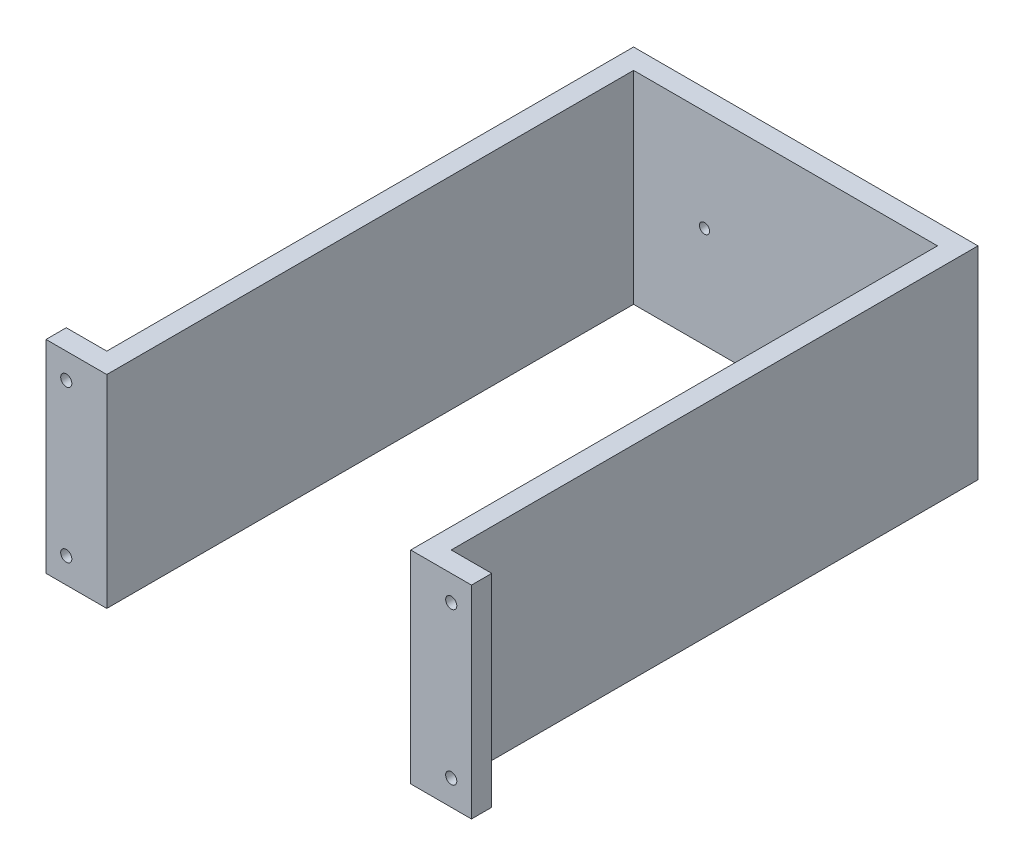
SolidWorks part; units mm, degrees
material "3003 Alloy"
ref_plane "Front Plane" through (0, 0, 0) normal (0, 0, 1) x (1, 0, 0)
ref_plane "Top Plane" through (0, 0, 0) normal (0, 1, 0) x (1, 0, 0)
ref_plane "Right Plane" through (0, 0, 0) normal (1, 0, 0) x (0, 0, -1)
sketch "Sketch1" plane through (0, 0, 0) normal (0, 1, 0) x (1, 0, 0)
  line L0 (0, 0) -> (30, 0)
  line L1 (30, 0) -> (30, 260)
  line L2 (30, 260) -> (180, 260)
  line L3 (180, 260) -> (180, 0)
  line L4 (180, 0) -> (210, 0)
  line L12 (0, 10) -> (20, 10)
  line L13 (20, 10) -> (20, 270)
  line L14 (20, 270) -> (190, 270)
  line L15 (190, 270) -> (190, 10)
  line L16 (190, 10) -> (210, 10)
  line L17 (0, 0) -> (0, 10)
  line L18 (210, 0) -> (210, 10)
  dimension "D1" = 20
  dimension "D2" = 260
  dimension "D3" = 150
  dimension "D4" = 10
extrude "Boss-Extrude1" add sketch "Sketch1" along normal blind 100
sketch "Sketch3" plane through (0, 0, -270) normal (0, 0, -1) x (-1, 0, 0)
  line L0 (-190, 100) -> (-20, 100) construction
  line L1 (-210, 100) -> (-210, 0) construction
  circle A0 centre (-105, 50) radius 4
  point P4 (-105, 100)
  point P7 (-210, 50)
  dimension "D1" = 8
sketch "Sketch4" plane through (0, 0, -270) normal (0, 0, -1) x (-1, 0, 0)
  line L0 (-190, 100) -> (-190, 0) construction
  line L1 (-20, 100) -> (-20, 0) construction
  line L2 (-190, 100) -> (-190, 0) construction
  point P0 (-145, 50)
  point P1 (-65, 50)
  point P7 (-190, 50)
  dimension "D1" = 45
  dimension "D2" = 45
hole_wizard "M6 Tapped Hole2" positions "Sketch7" profile "Sketch8" tap size "M6" standard "ISO"
sketch "Sketch7" plane through (0, 0, -270) normal (0, 0, -1) x (-1, 0, 0)
  point P0 (-145, 50)
  point P3 (-65, 50)
sketch "Sketch8" plane through (145, 50, -270) normal (1, 0, 0) x (0, 1, 0)
  line L0 (0, 0) -> (0, 15)
  line L1 (0, 15) -> (2.5, 13.4978)
  line L2 (2.5, 13.4978) -> (2.5, 0)
  line L5 (2.5, 0) -> (0, 0)
  line L10 (0, 15) -> (-2.5, 13.4978) construction
  line L11 (0, -6.35) -> (0, 107.95) construction
  dimension "Tap Drill Dia." = 5
  dimension "Tap Drill Depth" = 15
  dimension "Drill Angle" = 118
cosmetic thread "Hole Thread5" parameters "D1"=12, "D2"=6
cosmetic thread "Hole Thread6" parameters "D1"=12, "D2"=6
sketch "Sketch9" plane through (0, 0, -270) normal (0, 0, -1) x (-1, 0, 0)
  circle A0 centre (-145, 50) radius 6
  circle A1 centre (-65, 50) radius 6
  dimension "D1" = 12
extrude "Cut-Extrude2" cut sketch "Sketch9" against normal blind 2.6
sketch "Sketch10" plane through (0, 0, -10) normal (0, 0, -1) x (-1, 0, 0)
  line L0 (-210, 0) -> (-190, 0) construction
  line L1 (-20, 0) -> (0, 0) construction
  line L2 (-10, 87.5) -> (-10, 12.5) construction
  line L3 (-10, 12.5) -> (-200, 12.5) construction
  line L4 (-200, 12.5) -> (-200, 87.5) construction
  line L5 (-200, 87.5) -> (-10, 87.5) construction
  line L6 (0, 100) -> (0, 0) construction
  circle A0 centre (-10, 87.5) radius 2.75
  circle A1 centre (-10, 12.5) radius 2.75
  circle A2 centre (-200, 12.5) radius 2.75
  circle A3 centre (-200, 87.5) radius 2.75
  point P10 (-200, 0)
  point P13 (-10, 0)
  point P16 (0, 50)
  point P17 (-10, 50)
  dimension "D1" = 5.5
  dimension "D2" = 75
extrude "Cut-Extrude3" cut sketch "Sketch10" against normal through all
sketch "Sketch11" plane through (0, 0, -10) normal (0, 0, -1) x (-1, 0, 0)
  circle A0 centre (-10, 87.5) radius 5.5
  circle A1 centre (-10, 12.5) radius 5.5
  circle A2 centre (-200, 12.5) radius 5.5
  circle A3 centre (-200, 87.5) radius 5.5
  dimension "D1" = 11
extrude "Cut-Extrude4" cut sketch "Sketch11" against normal blind 5.5
